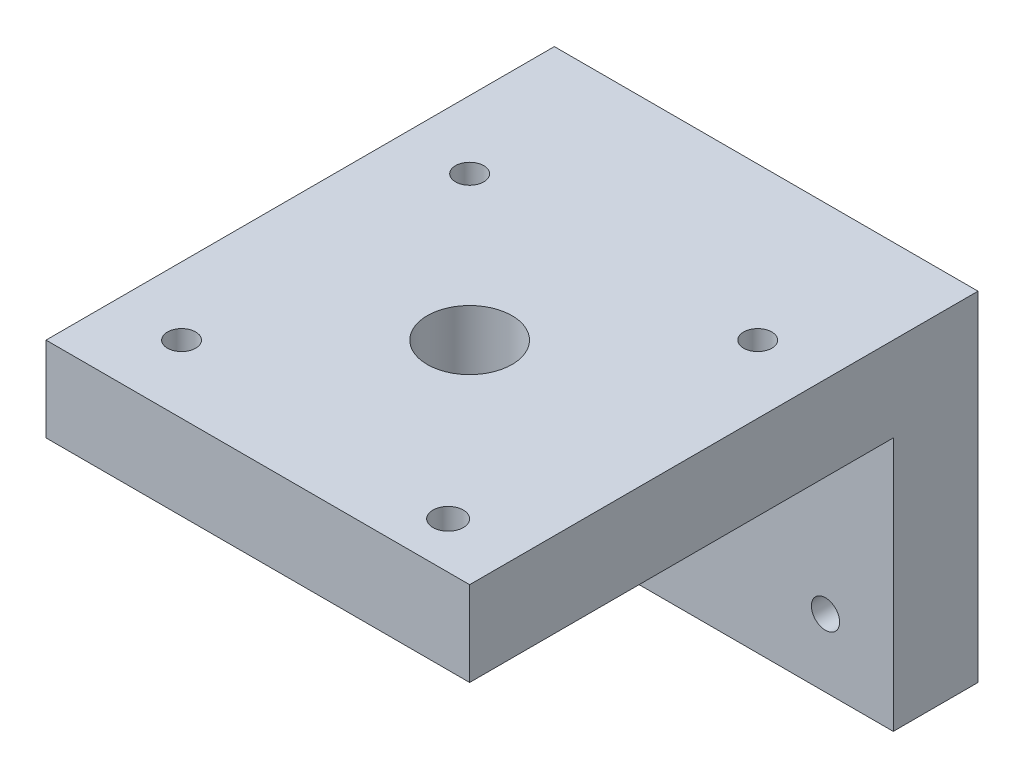
SolidWorks part; units mm, degrees
ref_plane "Front Plane" through (0, 0, 0) normal (0, 0, 1) x (1, 0, 0)
ref_plane "Top Plane" through (0, 0, 0) normal (0, 1, 0) x (1, 0, 0)
ref_plane "Right Plane" through (0, 0, 0) normal (1, 0, 0) x (0, 0, -1)
sketch "Sketch1" plane through (0, 0, 0) normal (0, 1, 0) x (1, 0, 0)
  line L1 (-25, -25) -> (25, -25)
  line L2 (-25, -25) -> (-25, 25)
  line L3 (-25, 25) -> (25, 25)
  line L4 (25, -25) -> (25, 25)
  line L5 (-25, -25) -> (25, 25) construction
  line L6 (-25, 25) -> (25, -25) construction
  circle A0 centre (0, 0) radius 5
  circle A1 centre (-17, 17) radius 1.666
  circle A2 centre (17, 17) radius 1.666
  circle A3 centre (-17, -17) radius 1.666
  circle A4 centre (17, -19.537) radius 1.7939
  dimension "D1" = 50
  dimension "D3" = 8
  dimension "D2" = 50
  dimension "D4" = 8
  dimension "D5" = 8
  dimension "D6" = 8
  dimension "D7" = 8
  dimension "D8" = 8
  dimension "D9" = 8
  dimension "D10" = 8
extrude "Boss-Extrude3" add sketch "Sketch1" along normal blind 10
sketch "Sketch2" plane through (0, 0, -25) normal (0, 0, -1) x (-1, 0, 0)
  line L1 (25, 0) -> (-25, 0)
  line L2 (25, 0) -> (25, 10)
  line L3 (25, 10) -> (-25, 10)
  line L4 (-25, 0) -> (-25, 10)
extrude "Boss-Extrude4" add sketch "Sketch2" along normal blind 10
sketch "Sketch3" plane through (0, 0, 0) normal (0, -1, 0) x (-1, 0, 0)
  line L0 (-25, -25) -> (-25, 35) construction
  line L1 (25, 35) -> (-25, 35)
  line L2 (25, 35) -> (25, 25)
  line L3 (25, 25) -> (-25, 25)
  line L4 (-25, 35) -> (-25, 25)
  dimension "D1" = 10
extrude "Boss-Extrude5" add sketch "Sketch3" along normal blind 30
sketch "Sketch4" plane through (0, 0, -25) normal (0, 0, 1) x (1, 0, 0)
  line L0 (25, -30) -> (-25, -30) construction
  line L1 (25, -30) -> (25, 0) construction
  line L2 (-25, -30) -> (-25, 0) construction
  line L3 (-25, -30) -> (25, -30) construction
  circle A0 centre (17, -22) radius 1.666
  circle A1 centre (0, -10) radius 1.666
  circle A2 centre (-17, -22) radius 1.666
  point P12 (0, -30)
  dimension "D1" = 8
  dimension "D2" = 8
  dimension "D3" = 8
  dimension "D4" = 8
  dimension "D5" = 20
  dimension "D6" = 25
extrude "Cut-Extrude1" cut sketch "Sketch4" against normal blind 30
sketch "Sketch5" plane through (0, 0, 0) normal (0, -1, 0) x (-1, 0, 0)
  circle A0 centre (0, 0) radius 5
